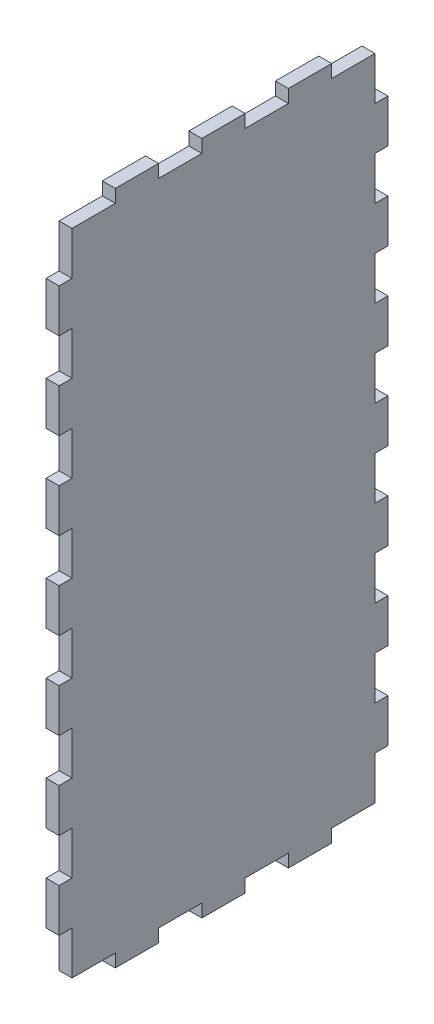
SolidWorks part; units mm, degrees
ref_plane "Front Plane" through (0, 0, 0) normal (0, 0, 1) x (1, 0, 0)
ref_plane "Top Plane" through (0, 0, 0) normal (0, 1, 0) x (1, 0, 0)
ref_plane "Right Plane" through (0, 0, 0) normal (1, 0, 0) x (0, 0, -1)
sketch "Sketch1" plane through (0, 0, 0) normal (1, 0, 0) x (0, 0, -1)
  line L1 (10, 153.0059) -> (20, 153.0059)
  line L2 (0, 140) -> (0, 150.0059)
  line L3 (0, 150.0059) -> (10, 150.0059)
  line L4 (10, 150.0059) -> (10, 153.0059)
  line L5 (-3, 120) -> (0, 120)
  line L6 (-3, 130) -> (-3, 140)
  line L7 (0, 130) -> (-3, 130)
  line L8 (0, 120) -> (0, 130)
  line L9 (-3, 100) -> (0, 100)
  line L10 (-3, 110) -> (-3, 120)
  line L11 (0, 110) -> (-3, 110)
  line L12 (-3, 140) -> (0, 140)
  line L13 (0, 100) -> (0, 110)
  line L14 (-3, 80) -> (0, 80)
  line L15 (-3, 90) -> (-3, 100)
  line L16 (0, 90) -> (-3, 90)
  line L17 (0, 80) -> (0, 90)
  line L18 (-3, 60) -> (0, 60)
  line L19 (-3, 70) -> (-3, 80)
  line L20 (0, 70) -> (-3, 70)
  line L21 (0, 60) -> (0, 70)
  line L22 (-3, 40) -> (0, 40)
  line L23 (-3, 50) -> (-3, 60)
  line L24 (0, 50) -> (-3, 50)
  line L25 (0, 40) -> (0, 50)
  line L26 (-3, 20) -> (0, 20)
  line L27 (-3, 30) -> (-3, 40)
  line L28 (0, 30) -> (-3, 30)
  line L29 (0, 20) -> (0, 30)
  line L30 (-3, 10) -> (-3, 20)
  line L31 (20, 153.0059) -> (20, 150.0059)
  line L32 (0, 10) -> (-3, 10)
  line L33 (0, 0) -> (0, 10)
  line L34 (20, 150.0059) -> (30, 150.0059)
  line L35 (30, 153.0059) -> (40, 153.0059)
  line L36 (30, 150.0059) -> (30, 153.0059)
  line L37 (40, 153.0059) -> (40, 150.0059)
  line L38 (40, 150.0059) -> (50, 150.0059)
  line L39 (50, 153.0059) -> (60, 153.0059)
  line L40 (50, 150.0059) -> (50, 153.0059)
  line L41 (60, 153.0059) -> (60, 150.0059)
  line L42 (60, 150.0059) -> (70, 150.0059)
  line L49 (70, 0) -> (70, 10)
  line L50 (70, 10) -> (73, 10)
  line L51 (73, 10) -> (73, 20)
  line L52 (70, 20) -> (70, 30)
  line L53 (70, 30) -> (73, 30)
  line L54 (73, 30) -> (73, 40)
  line L55 (73, 20) -> (70, 20)
  line L56 (70, 40) -> (70, 50)
  line L57 (70, 50) -> (73, 50)
  line L58 (73, 50) -> (73, 60)
  line L59 (73, 40) -> (70, 40)
  line L60 (70, 60) -> (70, 70)
  line L61 (70, 70) -> (73, 70)
  line L62 (73, 70) -> (73, 80)
  line L63 (73, 60) -> (70, 60)
  line L64 (70, 80) -> (70, 90)
  line L65 (70, 90) -> (73, 90)
  line L66 (73, 90) -> (73, 100)
  line L67 (73, 80) -> (70, 80)
  line L68 (70, 100) -> (70, 110)
  line L69 (73, 140) -> (70, 140)
  line L70 (70, 110) -> (73, 110)
  line L71 (73, 110) -> (73, 120)
  line L72 (73, 100) -> (70, 100)
  line L73 (70, 120) -> (70, 130)
  line L74 (70, 130) -> (73, 130)
  line L75 (73, 130) -> (73, 140)
  line L76 (73, 120) -> (70, 120)
  line L77 (70, 140) -> (70, 150.0059)
  line L80 (60, 0) -> (70, 0)
  line L81 (60, -3) -> (60, 0)
  line L82 (50, 0) -> (50, -3)
  line L83 (50, -3) -> (60, -3)
  line L84 (40, 0) -> (50, 0)
  line L85 (40, -3) -> (40, 0)
  line L86 (30, 0) -> (30, -3)
  line L87 (30, -3) -> (40, -3)
  line L88 (20, 0) -> (30, 0)
  line L89 (20, -3) -> (20, 0)
  line L90 (10, 0) -> (10, -3)
  line L91 (0, 0) -> (10, 0)
  line L92 (10, -3) -> (20, -3)
extrude "Boss-Extrude1" add sketch "Sketch1" along normal blind 3
